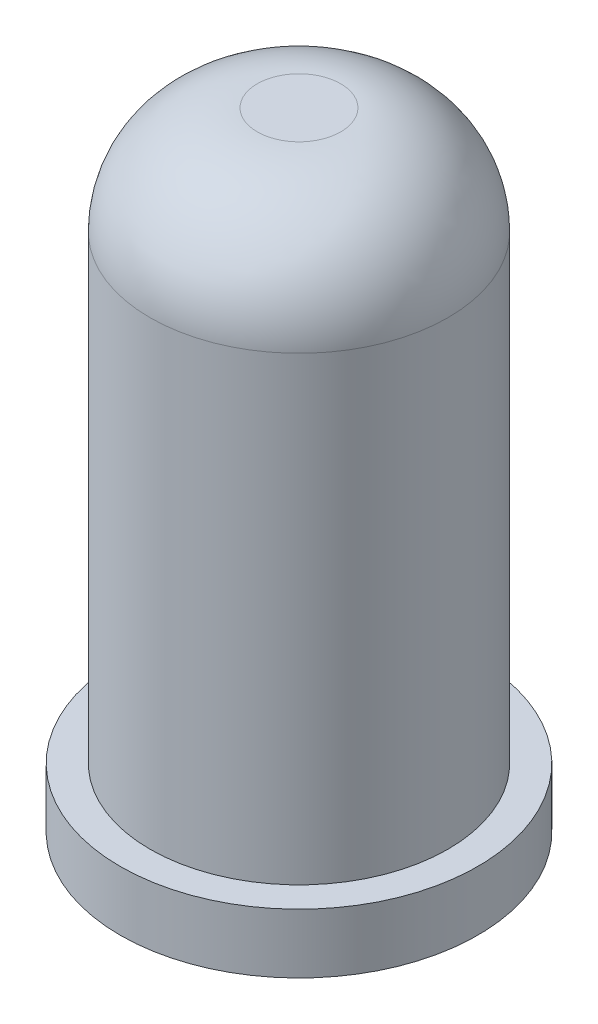
SolidWorks part; units mm, degrees
ref_plane "Front Plane" through (0, 0, 0) normal (0, 0, 1) x (1, 0, 0)
ref_plane "Top Plane" through (0, 0, 0) normal (0, 1, 0) x (1, 0, 0)
ref_plane "Right Plane" through (0, 0, 0) normal (1, 0, 0) x (0, 0, -1)
sketch "Sketch1" plane through (0, 0, 0) normal (0, 1, 0) x (1, 0, 0)
  circle A0 centre (0, 0) radius 2.5
  dimension "D1" = 5
extrude "Boss-Extrude1" add sketch "Sketch1" along normal blind 9.525
sketch "Sketch2" plane through (0, 0, 0) normal (0, -1, 0) x (1, 0, 0)
  circle A0 centre (0, 0) radius 3
extrude "Boss-Extrude2" add sketch "Sketch2" along normal blind 1
fillet "Fillet1" radius 1.8 1 edges at (0, 9.525, 2.5)
